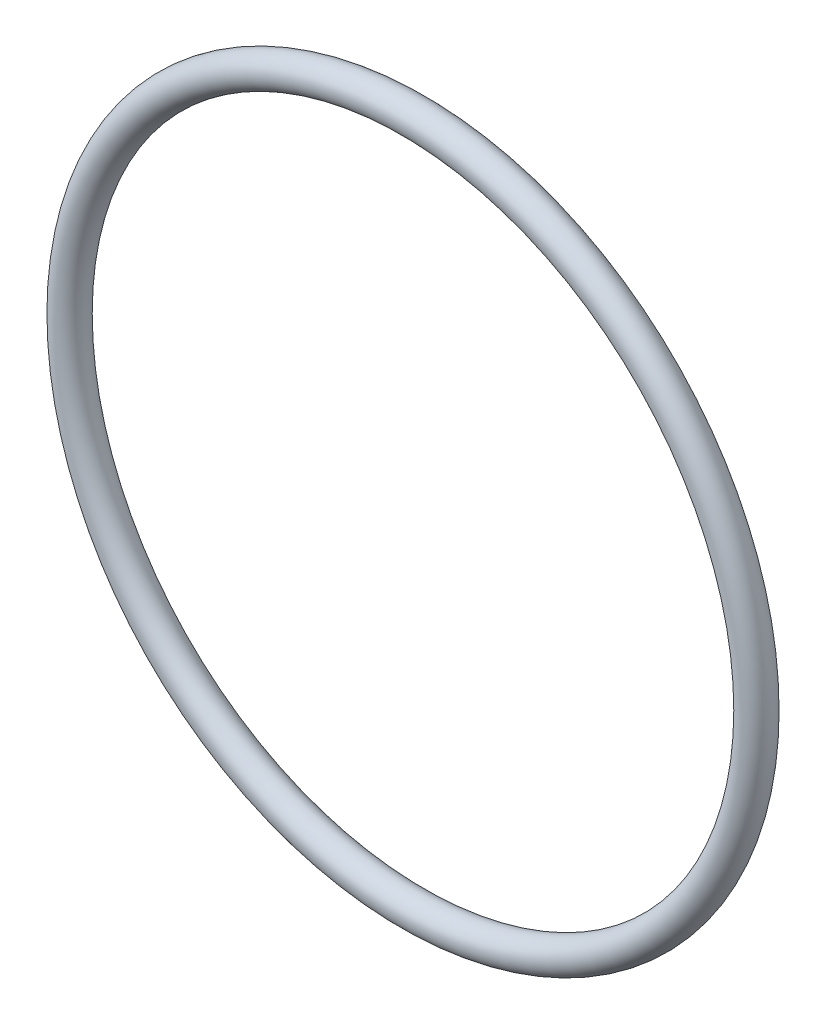
SolidWorks part; units mm, degrees
ref_plane "Front Plane" through (0, 0, 0) normal (0, 0, 1) x (1, 0, 0)
ref_plane "Top Plane" through (0, 0, 0) normal (0, 1, 0) x (1, 0, 0)
ref_plane "Right Plane" through (0, 0, 0) normal (1, 0, 0) x (0, 0, -1)
sketch "Sketch1" plane through (0, 0, 0) normal (0, 1, 0) x (1, 0, 0)
  line L0 (0, 0) -> (0, 3.1702) construction
  circle A0 centre (15, 0) radius 0.7
  dimension "D1" = 1.4
  dimension "D2" = 15
revolve "Revolve1" add sketch "Sketch1" angle 360 about L0
